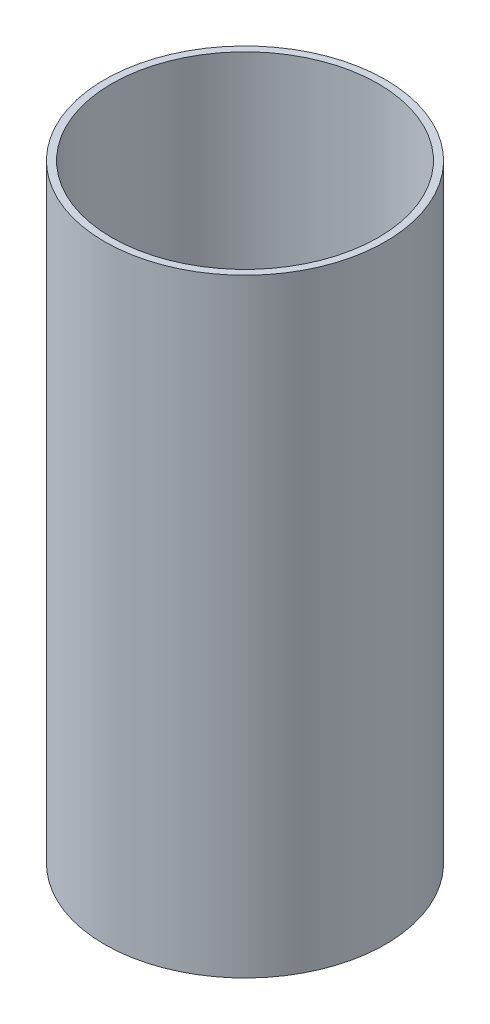
SolidWorks part; units mm, degrees
material "PVC Rigid"
ref_plane "Front Plane" through (0, 0, 0) normal (0, 0, 1) x (1, 0, 0)
ref_plane "Top Plane" through (0, 0, 0) normal (0, 1, 0) x (1, 0, 0)
ref_plane "Right Plane" through (0, 0, 0) normal (1, 0, 0) x (0, 0, -1)
sketch "Sketch1" plane through (0, 0, 0) normal (0, 1, 0) x (1, 0, 0)
  circle A0 centre (0, 0) radius 93.6625
  circle A1 centre (0, 0) radius 88.9
  dimension "D1" = 187.325
  dimension "D2" = 177.8
extrude "Boss-Extrude1" add sketch "Sketch1" along normal mid plane 405.9555
